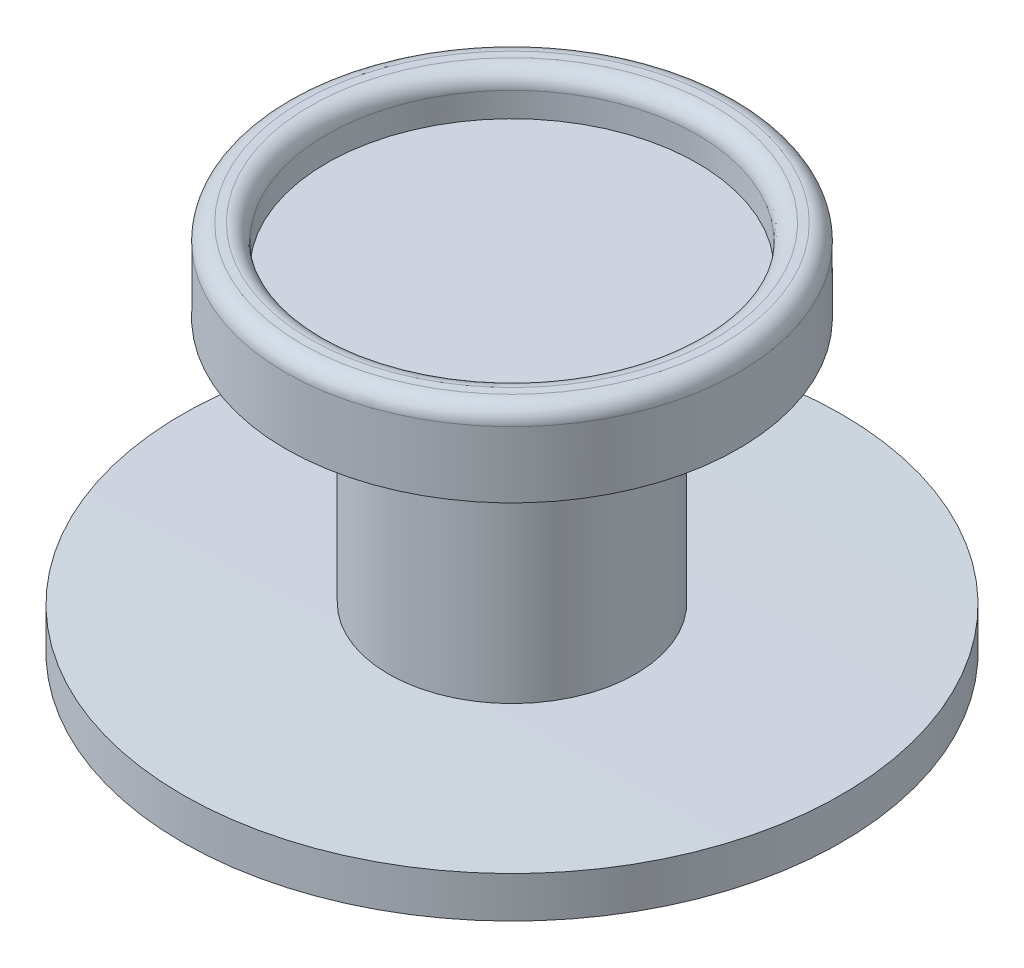
SolidWorks part; units mm, degrees
ref_plane "Plan de face" through (0, 0, 0) normal (0, 0, 1) x (1, 0, 0)
ref_plane "Plan de dessus" through (0, 0, 0) normal (0, 1, 0) x (1, 0, 0)
ref_plane "Plan de droite" through (0, 0, 0) normal (1, 0, 0) x (0, 0, -1)
sketch "Esquisse1" plane through (0, 0, 0) normal (0, 0, 1) x (1, 0, 0)
  line L0 (0, 39.0295) -> (0, -30.6525) construction
  line L1 (-1.5, -1.003) -> (-1.5, -4.003)
  line L2 (-4, -4.0216) -> (-4, -4.5216)
  line L3 (-2.25, -0.5068) -> (0, -0.5068)
  line L4 (-2.75, -1.0101) -> (-2.75, -0.0101)
  line L5 (-2.25, -0.5068) -> (-2.25, -0.0068)
  line L6 (0, -0.5068) -> (0, -5.0216)
  arc A0 (-1.5, -4.003) -> (-4, -4.0216) centre (0, -374) ccw
  arc A1 (-1.5, -1.003) -> (-2.75, -1.0101) centre (0, -374) ccw
  arc A2 (-2.25, -0.0068) -> (-2.75, -0.0101) centre (0, -374) ccw
  arc A3 (0, -5.0216) -> (-4, -4.5216) centre (0, 11.2284) cw
  dimension "D1" = 373
  dimension "D3" = 5.5
  dimension "D6" = 370
  dimension "D8" = 0.5
  dimension "D9" = 0.5
  dimension "D2" = 3
  dimension "D4" = 1
  dimension "D5" = 8
  dimension "D7" = 0.5
  dimension "D10" = 0.5
revolve "Révolution1" add sketch "Esquisse1" angle 360 about L0
fillet "Congé1" radius 0.2 2 edges at (0, -0.0101, 2.75) (0, -0.0068, 2.25)
